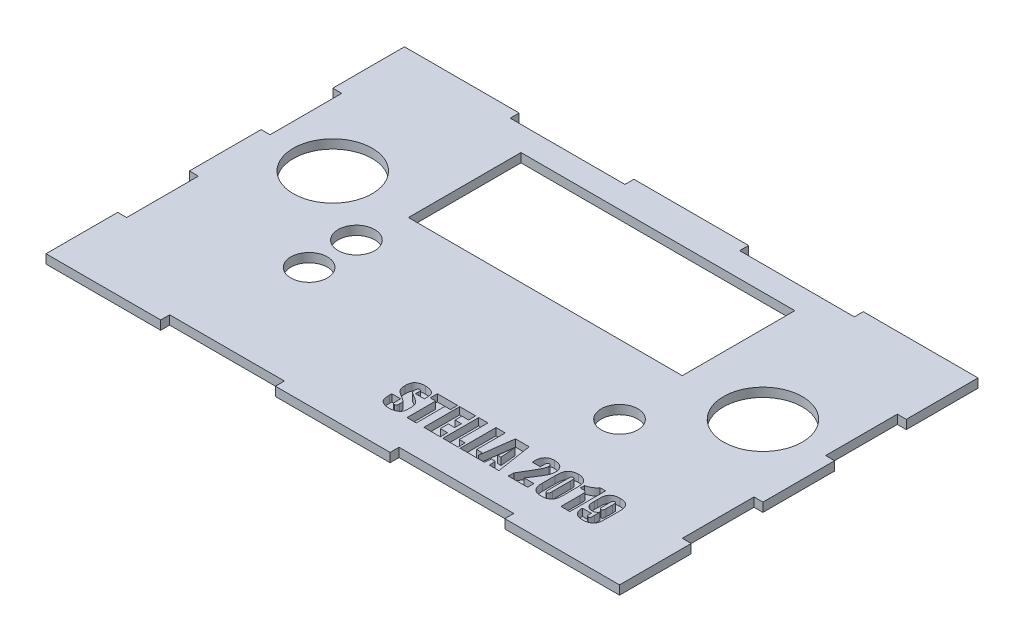
SolidWorks part; units mm, degrees
ref_plane "Front Plane" through (0, 0, 0) normal (0, 0, 1) x (1, 0, 0)
ref_plane "Top Plane" through (0, 0, 0) normal (0, 1, 0) x (1, 0, 0)
ref_plane "Right Plane" through (0, 0, 0) normal (1, 0, 0) x (0, 0, -1)
sketch "Sketch1" plane through (0, 0, 0) normal (0, 1, 0) x (1, 0, 0)
  line L1 (-101.6, -63.5) -> (101.6, -63.5)
  line L2 (-101.6, -63.5) -> (-101.6, 63.5)
  line L3 (-101.6, 63.5) -> (101.6, 63.5)
  line L4 (101.6, -63.5) -> (101.6, 63.5)
  line L5 (-101.6, -63.5) -> (101.6, 63.5) construction
  line L6 (-101.6, 63.5) -> (101.6, -63.5) construction
  point P0 (0, 0)
  dimension "D1" = 203.2
  dimension "D2" = 127
extrude "Boss-Extrude2" add sketch "Sketch1" along normal blind 3.175 contours L2 L1 L4 L3
sketch "Sketch2" plane through (0, 3.175, 0) normal (0, 1, 0) x (1, 0, 0)
  line L0 (-101.6, -63.5) -> (101.6, -63.5) construction
  line L1 (-60.96, -63.5) -> (-20.32, -63.5)
  line L2 (-60.96, -63.5) -> (-60.96, -60.325)
  line L3 (-60.96, -60.325) -> (-20.32, -60.325)
  line L4 (-20.32, -63.5) -> (-20.32, -60.325)
  dimension "D1" = 3.175
  dimension "D2" = 40.64
  dimension "D3" = 40.64
extrude "Cut-Extrude1" cut sketch "Sketch2" against normal blind 3.175
pattern_linear "LPattern2" count 2 spacing 81.28 along (1, 0, 0) of "Cut-Extrude1"
sketch "Sketch3" plane through (0, 3.175, 0) normal (0, 1, 0) x (1, 0, 0)
  line L0 (-101.6, -63.5) -> (-101.6, 63.5) construction
  line L1 (-101.6, -38.1) -> (-98.425, -38.1)
  line L2 (-101.6, -38.1) -> (-101.6, -12.7)
  line L3 (-101.6, -12.7) -> (-98.425, -12.7)
  line L4 (-98.425, -38.1) -> (-98.425, -12.7)
  dimension "D1" = 3.175
  dimension "D2" = 25.4
  dimension "D3" = 25.4
extrude "Cut-Extrude2" cut sketch "Sketch3" against normal blind 3.175
pattern_linear "LPattern3" count 2 spacing 50.8 along (0, 0, -1) of "Cut-Extrude2"
ref_plane "Plane1" through (101.6, 3.175, 63.5) normal (0, 0, -1) x (-1, 0, 0)
sketch "Sketch6" plane through (0, 3.175, 0) normal (0, 1, 0) x (1, 0, 0)
  line L0 (101.6, -63.5) -> (101.6, 63.5) construction
  line L1 (101.6, -38.1) -> (98.425, -38.1)
  line L2 (101.6, -38.1) -> (101.6, -12.7)
  line L3 (101.6, -12.7) -> (98.425, -12.7)
  line L4 (98.425, -38.1) -> (98.425, -12.7)
  line L5 (108.585, -63.5) -> (94.615, -63.5) construction
  dimension "D1" = 25.4
  dimension "D2" = 25.4
  dimension "D3" = 3.175
extrude "Cut-Extrude3" cut sketch "Sketch6" against normal blind 3.175
pattern_linear "LPattern4" count 2 spacing 50.8 along (0, 0, -1) of "Cut-Extrude3"
sketch "Sketch7" plane through (0, 3.175, 0) normal (0, 1, 0) x (1, 0, 0)
  line L0 (-101.6, 63.5) -> (101.6, 63.5) construction
  line L2 (-60.96, 63.5) -> (-20.32, 63.5)
  line L3 (-60.96, 63.5) -> (-60.96, 60.325)
  line L4 (-60.96, 60.325) -> (-20.32, 60.325)
  line L5 (-20.32, 63.5) -> (-20.32, 60.325)
  dimension "D1" = 40.64
  dimension "D2" = 3.175
  dimension "D3" = 40.64
extrude "Cut-Extrude5" cut sketch "Sketch7" against normal blind 3.175 contours L3 L2 L5 L4
pattern_linear "LPattern6" count 2 spacing 81.28 along (1, 0, 0) of "Cut-Extrude5"
sketch "Sketch9" plane through (0, 3.175, 0) normal (0, 1, 0) x (1, 0, 0)
  line L0 (0, 0) -> (0, 63.5) construction
  line L1 (-20.32, 63.5) -> (20.32, 63.5) construction
  line L3 (-48.514, 11.811) -> (48.514, 11.811)
  line L4 (-48.514, 11.811) -> (-48.514, 51.689)
  line L5 (-48.514, 51.689) -> (48.514, 51.689)
  line L6 (48.514, 11.811) -> (48.514, 51.689)
  line L7 (-48.514, 11.811) -> (48.514, 51.689) construction
  line L8 (-48.514, 51.689) -> (48.514, 11.811) construction
  point P5 (0, 31.75)
  dimension "D1" = 97.028
  dimension "D2" = 39.878
extrude "Cut-Extrude6" cut sketch "Sketch9" against normal blind 3.175
sketch "Sketch10" plane through (0, 3.175, 0) normal (0, 1, 0) x (1, 0, 0)
  line L0 (-101.6, -63.5) -> (-76.2, -63.5) construction
  line L1 (-101.6, -63.5) -> (-60.96, -63.5) construction
  line L2 (-76.2, -63.5) -> (-76.2, 12.7) construction
  circle A0 centre (-76.2, 12.7) radius 13.97
  dimension "D1" = 27.94
extrude "Cut-Extrude7" cut sketch "Sketch10" against normal blind 3.175
sketch "Sketch11" plane through (0, 3.175, 0) normal (0, 1, 0) x (1, 0, 0)
  line L0 (101.6, -38.1) -> (101.6, -88.9) construction
  line L1 (101.6, -63.5) -> (50.8, -63.5) construction
  line L2 (50.8, -63.5) -> (50.8, -12.7) construction
  line L3 (76.2, -63.5) -> (76.2, 12.7)
  line L10 (50.8, -12.7) -> (83.9418, -12.7) construction
  line L11 (-101.6, -63.5) -> (-50.8, -63.5) construction
  line L12 (-50.8, -12.7) -> (-50.8, -4.318) construction
  line L13 (-50.8, -12.7) -> (-50.8, -21.082) construction
  circle A0 centre (76.2, 12.7) radius 13.97
  circle A1 centre (-50.8, -4.318) radius 6.477
  circle A2 centre (-50.8, -21.082) radius 6.477
  circle A3 centre (50.8, -12.7) radius 6.477
  dimension "D3" = 27.94
sketch "Sketch12" plane through (0, 3.175, 0) normal (0, 1, 0) x (1, 0, 0)
  line L0 (101.6, -50.8) -> (0, -50.8) construction
  line L2 (81.28, -63.5) -> (81.28, 40.6323) construction
  text T0 "STELLA 2019" font "Impact" height 12.7
extrude "Cut-Extrude15" cut sketch "Sketch11" against normal blind 3.175
extrude "Cut-Extrude16" cut sketch "Sketch12" against normal blind 2.54
